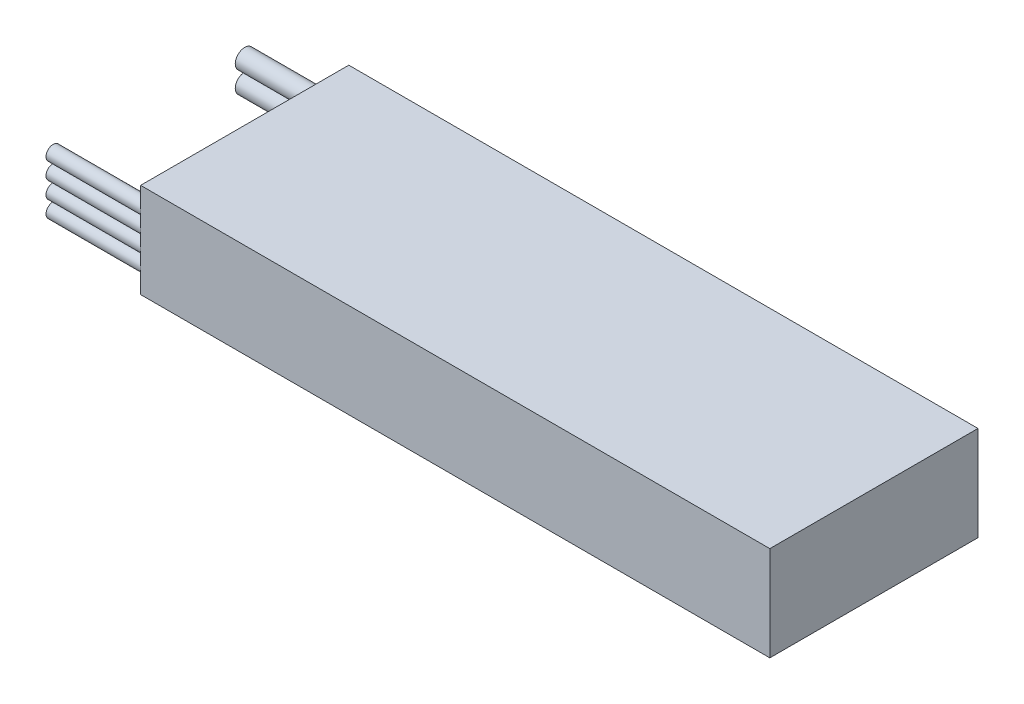
SolidWorks part; units mm, degrees
ref_plane "Front Plane" through (0, 0, 0) normal (0, 0, 1) x (1, 0, 0)
ref_plane "Top Plane" through (0, 0, 0) normal (0, 1, 0) x (1, 0, 0)
ref_plane "Right Plane" through (0, 0, 0) normal (1, 0, 0) x (0, 0, -1)
sketch "Sketch1" plane through (0, 0, 0) normal (0, 1, 0) x (1, 0, 0)
  line L1 (-66.5, 22) -> (66.5, 22)
  line L2 (-66.5, 22) -> (-66.5, -22)
  line L3 (-66.5, -22) -> (66.5, -22)
  line L4 (66.5, 22) -> (66.5, -22)
  line L5 (-66.5, 22) -> (66.5, -22) construction
  line L6 (-66.5, -22) -> (66.5, 22) construction
  point P0 (0, 0)
  dimension "D1" = 44
  dimension "D2" = 133
extrude "Boss-Extrude1" add sketch "Sketch1" along normal blind 20
sketch "Sketch2" plane through (-66.5, 0, 0) normal (-1, 0, 0) x (0, 0, 1)
  line L0 (-22, 20) -> (-20, 12.25)
  line L1 (-22, 0) -> (-20, 7.75)
  line L2 (-20, 12.25) -> (-20, 7.75)
  line L3 (-22, 20) -> (-22, 0) construction
  line L4 (22, 20) -> (20.5, 15.25)
  line L5 (20.5, 15.25) -> (20.5, 11.75)
  line L6 (20.5, 11.75) -> (20.5, 8.25)
  line L7 (20.5, 8.25) -> (20.5, 4.75)
  line L8 (20.5, 4.75) -> (22, 0)
  line L9 (22, 20) -> (22, 0) construction
  circle A0 centre (-20, 12.25) radius 2
  circle A1 centre (-20, 7.75) radius 2
  circle A2 centre (20.5, 15.25) radius 1.5
  circle A3 centre (20.5, 11.75) radius 1.5
  circle A4 centre (20.5, 8.25) radius 1.5
  circle A5 centre (20.5, 4.75) radius 1.5
  point P18 (22, 0)
  dimension "D1" = 4
  dimension "D2" = 3
  dimension "D3" = 4.5
  dimension "D4" = 3.5
extrude "Boss-Extrude3" add sketch "Sketch2" along normal blind 20 contours L2 A0 L0 | L0 A0 L2 | L2 A1 L1 | L1 A1 L2 | A2 L4 L5 | L4 A2 L5 | A3 L5 L6 | L5 A3 L6 | A4 L6 L7 | L6 A4 L7 | A5 L7 L8 | L7 A5 L8
